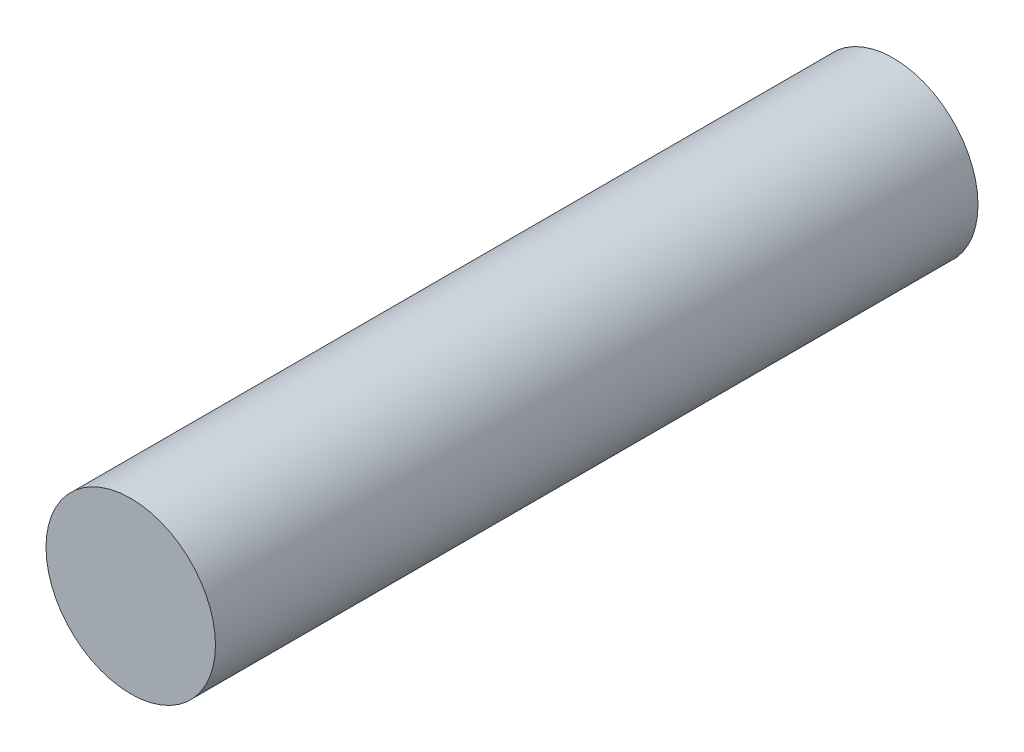
SolidWorks part; units mm, degrees
ref_plane "Front Plane" through (0, 0, 0) normal (0, 0, 1) x (1, 0, 0)
ref_plane "Top Plane" through (0, 0, 0) normal (0, 1, 0) x (1, 0, 0)
ref_plane "Right Plane" through (0, 0, 0) normal (1, 0, 0) x (0, 0, -1)
sketch "Sketch1" plane through (0, 0, 0) normal (0, 0, 1) x (1, 0, 0)
  circle A0 centre (0, 0) radius 3.175
  dimension "D1" = 6.35
extrude "Boss-Extrude1" add sketch "Sketch1" along normal mid plane 28.575
